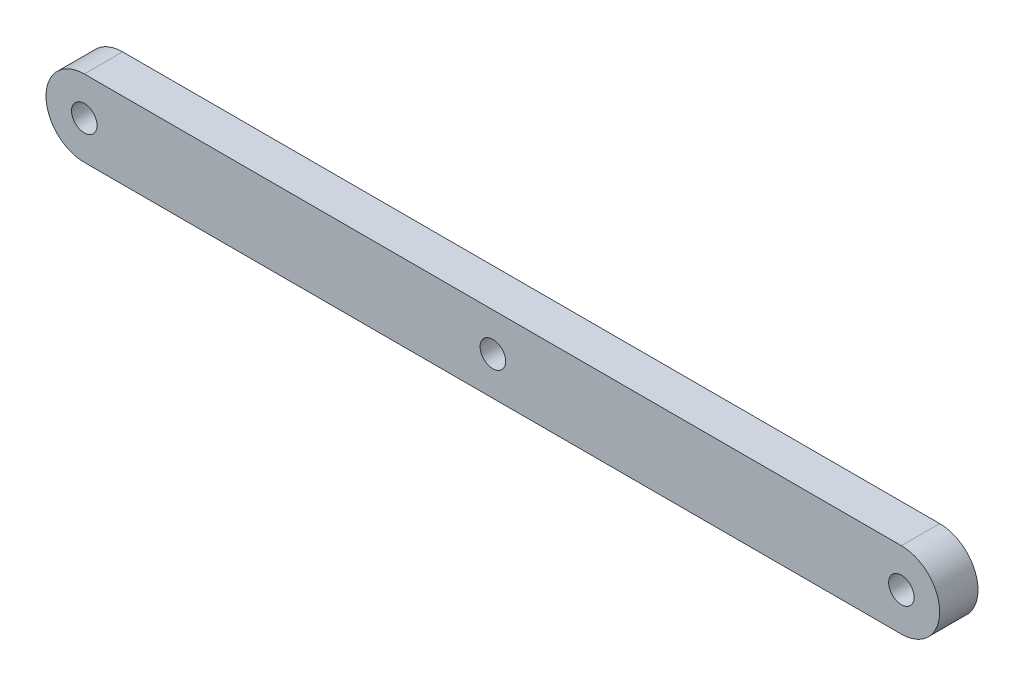
SolidWorks part; units mm, degrees
ref_plane "Front" through (0, 0, 0) normal (0, 0, 1) x (1, 0, 0)
ref_plane "Top" through (0, 0, 0) normal (0, 1, 0) x (1, 0, 0)
ref_plane "Right" through (0, 0, 0) normal (1, 0, 0) x (0, 0, -1)
sketch "草图1" plane through (0, 0, 0) normal (0, 0, 1) x (1, 0, 0)
  line L1 (-11, -2) -> (53, -2)
  line L3 (-11, 4) -> (53, 4)
  arc A0 (-11, 4) -> (-11, -2) centre (-11, 1) ccw
  arc A1 (53, -2) -> (53, 4) centre (53, 1) ccw
  circle A2 centre (-11, 1) radius 1
  circle A3 centre (53, 1) radius 1
  circle A4 centre (21, 1) radius 1
  point P4 (21, 4)
extrude "凸台-拉伸1" add sketch "草图1" along normal blind 3
